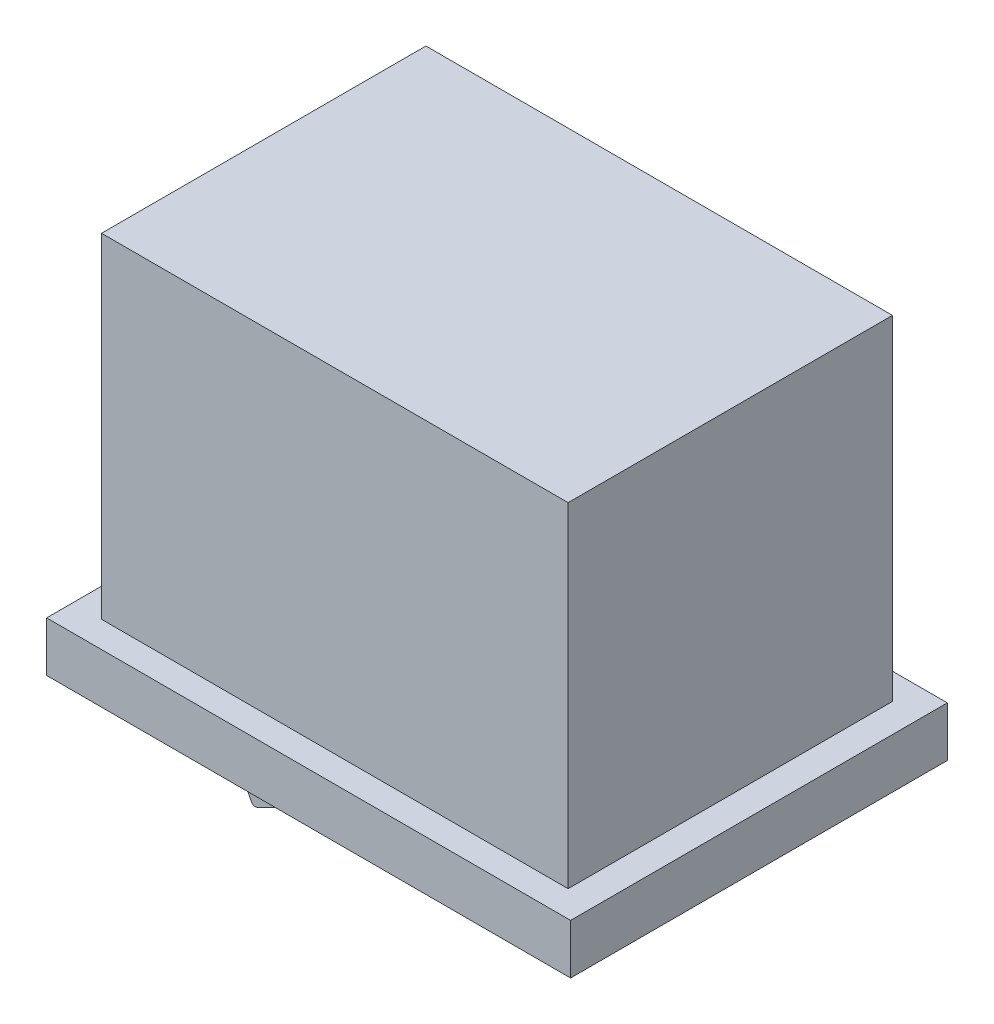
SolidWorks part; units mm, degrees
ref_plane "Front Plane" through (0, 0, 0) normal (0, 0, 1) x (1, 0, 0)
ref_plane "Top Plane" through (0, 0, 0) normal (0, 1, 0) x (1, 0, 0)
ref_plane "Right Plane" through (0, 0, 0) normal (1, 0, 0) x (0, 0, -1)
sketch "Sketch1" plane through (0, 0, 0) normal (0, 0, 1) x (1, 0, 0)
  line L1 (0, 0) -> (21, 0)
  line L2 (0, 0) -> (0, -15.4)
  line L3 (0, -15.4) -> (21, -15.4)
  line L4 (21, 0) -> (21, -15.4)
  line L5 (0, 0) -> (21, -15.4) construction
  line L6 (0, -15.4) -> (21, 0) construction
  point P4 (10.5, -7.7)
  dimension "D1" = 15.4
  dimension "D2" = 21
extrude "Boss-Extrude1" add sketch "Sketch1" along normal blind 15.1
sketch "Sketch3" plane through (0, 0, 0) normal (0, 1, 0) x (1, 0, 0)
  line L0 (21, 0) -> (0, 0) construction
  line L1 (19.85, -1.05) -> (1.15, -1.05)
  line L2 (19.85, -1.05) -> (19.85, -14.05)
  line L3 (19.85, -14.05) -> (1.15, -14.05)
  line L4 (1.15, -1.05) -> (1.15, -14.05)
  line L5 (19.85, -1.05) -> (1.15, -14.05) construction
  line L6 (19.85, -14.05) -> (1.15, -1.05) construction
  line L8 (21, -15.1) -> (21, 0) construction
  line L11 (0, -15.1) -> (21, -15.1)
  line L12 (0, -15.1) -> (0, 0)
  line L13 (0, 0) -> (21, 0)
  line L14 (21, -15.1) -> (21, 0)
  line L15 (0, -15.1) -> (21, 0) construction
  line L16 (0, 0) -> (21, -15.1) construction
  point P4 (10.5, -7.55)
  point P9 (10.5, -7.55)
  dimension "D1" = 18.7
  dimension "D2" = 13
  dimension "D3" = 1.05
  dimension "D4" = 1.15
extrude "Cut-Extrude1" cut sketch "Sketch3" against normal blind 13.4
sketch "Sketch4" plane through (0, -15.4, 0) normal (0, -1, 0) x (1, 0, 0)
  line L0 (0, 15.1) -> (21, 15.1) construction
  line L1 (1.5, 12.55) -> (19.5, 12.55)
  line L2 (1.5, 12.55) -> (1.5, 2.55)
  line L3 (1.5, 2.55) -> (19.5, 2.55)
  line L4 (19.5, 12.55) -> (19.5, 2.55)
  line L5 (1.5, 12.55) -> (19.5, 2.55) construction
  line L6 (1.5, 2.55) -> (19.5, 12.55) construction
  line L8 (0, 15.1) -> (0, 0) construction
  point P4 (10.5, 7.55)
  dimension "D1" = 10
  dimension "D2" = 18
  dimension "D3" = 2.55
  dimension "D4" = 1.5
extrude "Boss-Extrude2" add sketch "Sketch4" along normal blind 3
sketch "Sketch5" plane through (0, 0, 2.55) normal (0, 0, -1) x (-1, 0, 0)
  line L0 (-4.3182, -15.4) -> (-5.6403, -18.209)
  line L1 (-1.5, -15.4) -> (-19.5, -15.4) construction
  line L2 (-4.3182, -15.4) -> (-0.8084, -15.4)
  line L4 (-0.8084, -15.4) -> (-0.3356, -21.0603)
  line L5 (-0.3356, -21.0603) -> (-11.9118, -20.3604)
  line L6 (-11.9118, -20.3604) -> (-18.8261, -20.1571)
  line L7 (-18.8261, -20.1571) -> (-20.6757, -18.6624)
  line L8 (-20.6757, -18.6624) -> (-20.2286, -15.6064)
  line L9 (-20.2286, -15.6064) -> (-19.5, -15.4)
  line L10 (-19.5, -15.4) -> (-17.2007, -15.4)
  arc A0 (-5.6403, -18.209) -> (-5.9153, -18.3003) centre (-5.8212, -18.1238) cw
  spline S0 degree 3 poles (-5.9153, -18.3003) (-9.4142, -16.4339) (-13.181, -15.4655) (-17.2007, -15.4) knots 0.017358 0.017358 0.017358 0.017358 1 1 1 1
  dimension "D1" = 0.2
extrude "Cut-Extrude2" cut sketch "Sketch5" against normal through all
